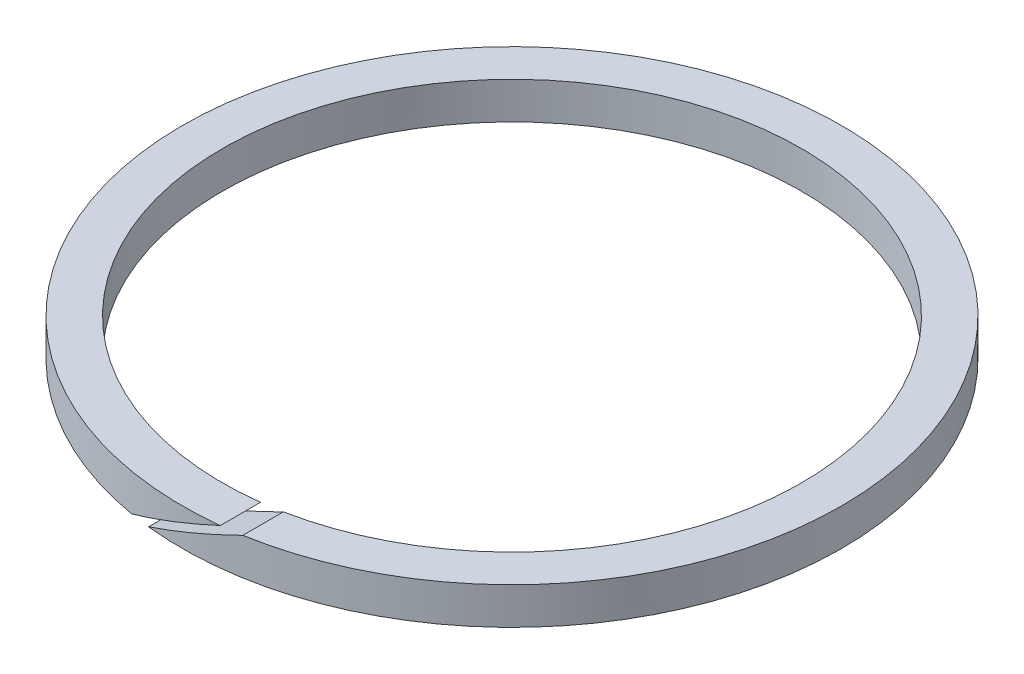
SolidWorks part; units mm, degrees
ref_plane "Front Plane" through (0, 0, 0) normal (0, 0, 1) x (1, 0, 0)
ref_plane "Top Plane" through (0, 0, 0) normal (0, 1, 0) x (1, 0, 0)
ref_plane "Right Plane" through (0, 0, 0) normal (1, 0, 0) x (0, 0, -1)
sketch "Sketch1" plane through (0, 0, 0) normal (0, 1, 0) x (1, 0, 0)
  line L0 (0, -9.7536) -> (0, -11.0998) construction
  circle A0 centre (0, 0) radius 9.7536 construction
  circle A1 centre (0, 0) radius 11.0998 construction
  dimension "ID" = 19.5072
  dimension "OD" = 22.1996
  dimension "Width" = 1.3462
sketch "Sketch2" plane through (0, 0, 0) normal (1, 0, 0) x (0, 0, -1)
  line L0 (0, 0.6223) -> (0, -0.6223) construction
  line L2 (11.0998, 0) -> (-11.0998, 0) construction
  point P5 (0, 0)
  dimension "Thickness" = 1.2446
sketch "Sketch3" plane through (0, 0, 0) normal (0, 1, 0) x (1, 0, 0)
  circle A0 centre (0, 0) radius 11.0998 construction
  circle A1 centre (0, 0) radius 11.0998
  circle A2 centre (0, 0) radius 9.7536 construction
  circle A3 centre (0, 0) radius 9.7536
extrude "Boss-Extrude1" add sketch "Sketch3" against normal up to vertex (0.6223 mm away) and the other way up to vertex (0.6223 mm away) up to point (0, -0.6223, 0) other way up to point (0, 0.6223, 0)
sketch "Sketch4" plane through (0, 0, 0) normal (0, 0, 1) x (1, 0, 0)
  line L0 (2.8849, 1.1656) -> (-2.8849, -1.1656) construction
  line L1 (11.0998, 0) -> (-11.0998, 0) construction
  line L2 (2.8383, 1.281) -> (-2.9316, -1.0502)
  line L3 (2.9316, 1.0502) -> (-2.8383, -1.281)
  line L4 (2.8383, 1.281) -> (2.9316, 1.0502)
  line L5 (-2.9316, -1.0502) -> (-2.8383, -1.281)
  dimension "D1" = 22
  dimension "D4" = 6.223
  dimension "D2" = 0.1245
  dimension "D3" = 0.1245
extrude "Cut-Extrude1" cut sketch "Sketch4" along normal through all
equation "\"D3@Sketch4\"=\"D2@Sketch4\""
equation "\"D2@Sketch4\"=\"Thickness@Sketch2\"/10"
equation "\"D4@Sketch4\"=\"Thickness@Sketch2\"*5"
